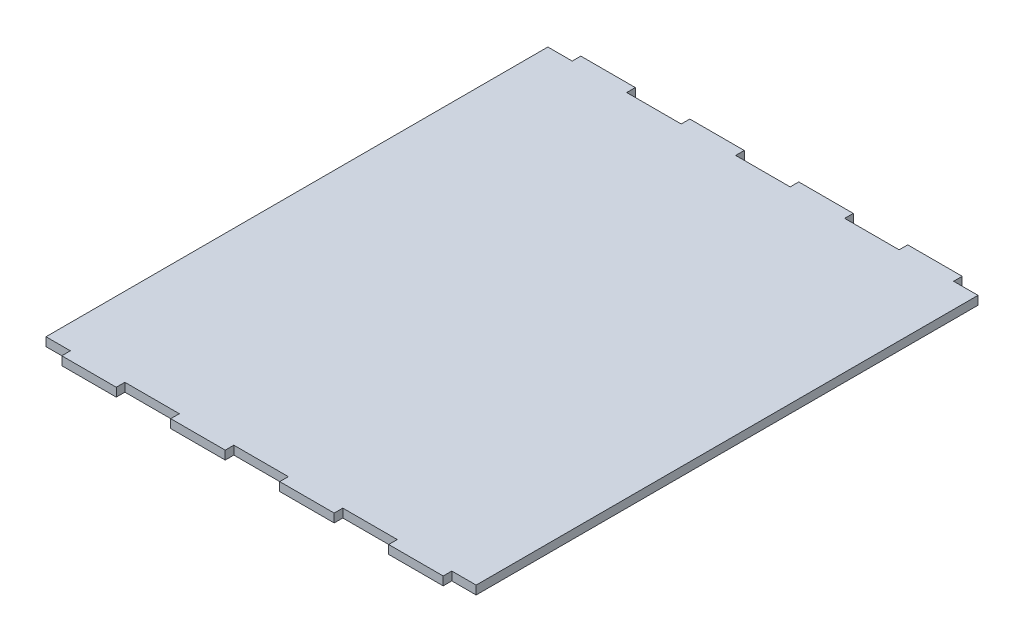
SolidWorks part; units mm, degrees
ref_plane "Front Plane" through (0, 0, 0) normal (0, 0, 1) x (1, 0, 0)
ref_plane "Top Plane" through (0, 0, 0) normal (0, 1, 0) x (1, 0, 0)
ref_plane "Right Plane" through (0, 0, 0) normal (1, 0, 0) x (0, 0, -1)
sketch "Sketch1" plane through (0, 0, 0) normal (0, 1, 0) x (1, 0, 0)
  line L0 (46.5, 181) -> (65.5, 181)
  line L1 (8.5, 0) -> (27.5, 0)
  line L2 (0, 3) -> (0, 178)
  line L3 (8.5, 181) -> (27.5, 181)
  line L4 (150, 3) -> (150, 178)
  line L6 (8.5, 181) -> (8.5, 178)
  line L7 (8.5, 178) -> (0, 178)
  line L9 (27.5, 178) -> (46.5, 178)
  line L10 (27.5, 178) -> (27.5, 181)
  line L12 (46.5, 178) -> (46.5, 181)
  line L13 (65.5, 178) -> (84.5, 178)
  line L14 (65.5, 178) -> (65.5, 181)
  line L16 (84.5, 178) -> (84.5, 181)
  line L17 (84.5, 181) -> (103.5, 181)
  line L18 (122.5, 181) -> (141.5, 181)
  line L20 (103.5, 181) -> (103.5, 178)
  line L21 (103.5, 178) -> (122.5, 178)
  line L22 (122.5, 181) -> (122.5, 178)
  line L24 (141.5, 181) -> (141.5, 178)
  line L25 (141.5, 178) -> (150, 178)
  line L29 (0, 3) -> (8.5, 3)
  line L30 (8.5, 0) -> (8.5, 3)
  line L31 (46.5, 0) -> (65.5, 0)
  line L33 (27.5, 0) -> (27.5, 3)
  line L34 (27.5, 3) -> (46.5, 3)
  line L35 (46.5, 0) -> (46.5, 3)
  line L37 (65.5, 0) -> (65.5, 3)
  line L38 (65.5, 3) -> (84.5, 3)
  line L39 (84.5, 0) -> (84.5, 3)
  line L41 (103.5, 0) -> (103.5, 3)
  line L42 (103.5, 3) -> (122.5, 3)
  line L43 (122.5, 0) -> (122.5, 3)
  line L45 (141.5, 0) -> (141.5, 3)
  line L46 (141.5, 3) -> (150, 3)
  line L48 (84.5, 0) -> (103.5, 0)
  line L49 (122.5, 0) -> (141.5, 0)
  line L50 (0, 0) -> (0, 3) construction
  point P3 (0, 0)
  dimension "D1" = 150
  dimension "D2" = 8.5
  dimension "D3" = 3
  dimension "19" = 19
  dimension "D4" = 3
  dimension "D5" = 8.5
  dimension "D6" = 19
  dimension "D7" = 181
extrude "Boss-Extrude1" add sketch "Sketch1" along normal blind 3 contours L2 L7 L6 L3 L10 L9 L12 L0 L14 L13 L16 L17 L20 L21 L22 L18 L24 L25 L4 L46 L45 L49 L43 L42 L41 L48 L39 L38 L37 L31 L35 L34 L33 L1 L30 L29
